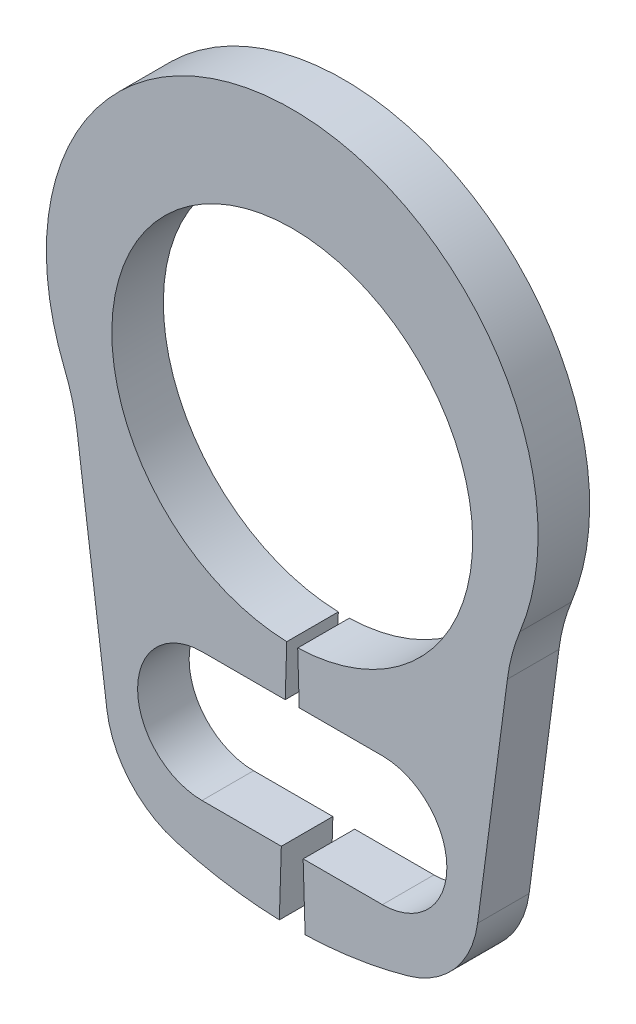
SolidWorks part; units mm, degrees
ref_plane "Plane1" through (0, 0, 0) normal (0, 0, 1) x (1, 0, 0)
ref_plane "Plane2" through (0, 0, 0) normal (0, 1, 0) x (1, 0, 0)
ref_plane "Plane3" through (0, 0, 0) normal (1, 0, 0) x (0, 0, -1)
sketch "Clipboard" plane through (0, 0, 0) normal (0, 0, 1) x (1, 0, 0)
  line L0 (0, 0) -> (0.8, 0)
  line L1 (0, 0) -> (0, 0.4)
  line L2 (0, 0) -> (0, -1.9)
  circle A0 centre (0, 0) radius 0.5
  circle A1 centre (0, 0) radius 1.5
  dimension "HoleDia" = 1
  dimension "ShaftDia" = 3
  dimension "LargeSection" = 0.8
  dimension "SmallSection" = 0.4
  dimension "LugSection" = 1.9
sketch "BodySke" plane through (0, 0, 0) normal (0, 0, 1) x (1, 0, 0)
  line L0 (-1.5431, 0) -> (1.5431, 0) construction
  line L1 (0, 0) -> (0, 2.2) construction
  line L2 (0.0424, -1.3994) -> (0.1, -3.2985)
  line L3 (-0.0424, -1.3994) -> (-0.1, -3.2985)
  line L4 (0, 0) -> (3.148, -0.99) construction
  line L5 (0, 0) -> (-3.148, -0.99) construction
  line L7 (1.6697, -0.7954) -> (1.4386, -2.5514)
  line L8 (-1.6697, -0.7954) -> (-1.4386, -2.5514)
  circle A0 centre (0, 0) radius 1.4 construction
  arc A1 (0.0424, -1.3994) -> (-0.0424, -1.3994) centre (0, 0) ccw
  arc A2 (1.7171, -0.54) -> (-1.7171, -0.54) centre (0, 0.292) ccw construction
  arc A3 (0.1, -3.2985) -> (0.8994, -3.1751) centre (0, 0) ccw
  arc A4 (1.7671, -0.4277) -> (1.6697, -0.7954) centre (3.148, -0.99) ccw
  arc A5 (-1.6697, -0.7954) -> (-1.7671, -0.4277) centre (-3.148, -0.99) ccw
  arc A6 (-0.8994, -3.1751) -> (-0.1, -3.2985) centre (0, 0) ccw
  arc A7 (1.7671, -0.4277) -> (-1.7671, -0.4277) centre (0, 0.292) ccw
  arc A8 (-1.5312, -1.8481) -> (1.5312, -1.8481) centre (0, 0) ccw construction
  circle A9 centre (0.7, -2.2956) radius 0.5
  circle A10 centre (-0.7, -2.2956) radius 0.5
  arc A11 (1.4386, -2.5514) -> (0.8994, -3.1751) centre (0.695, -2.4535) cw
  arc A12 (-1.4386, -2.5514) -> (-0.8994, -3.1751) centre (-0.695, -2.4535) ccw
  point P28 (1.3798, -2.9977)
  point P31 (-1.3798, -2.9977)
  dimension "GrooveDia" = 2.8
  dimension "D3" = 0.75
  dimension "LugRad" = 3.3
  dimension "HoleOffsetRad" = 2.4
  dimension "HoleDia" = 1
  dimension "D2" = 15
  dimension "LargeRad" = 2.2
  dimension "SmallRad" = 1.8
  dimension "Gap" = 0.2
  dimension "SmallAngle" = 145.083
  dimension "HoleSpacing" = 1.4
extrude "Body" add sketch "BodySke" against normal blind 0.4
sketch "NotSke" plane through (0, 0, 0) normal (0, 0, 1) x (1, 0, 0)
  line L0 (0.7, -1.7956) -> (0.7, -2.7956)
  line L1 (0.7, -2.7956) -> (-0.7, -2.7956)
  line L2 (-0.7, -2.7956) -> (-0.7, -1.7956)
  line L3 (-0.7, -1.7956) -> (0.7, -1.7956)
  circle A0 centre (0.7, -2.2956) radius 0.5 construction
  circle A1 centre (-0.7, -2.2956) radius 0.5 construction
extrude "Notch" cut sketch "NotSke" against normal through all
sketch "UnlSke" plane through (0, 0, 0) normal (0, 0, 1) x (1, 0, 0)
  line L0 (-1.599, -2.8867) -> (-0.6784, -1.2247)
  line L1 (1.599, -2.8867) -> (0.6784, -1.2247)
  arc A0 (0.6784, -1.2247) -> (-0.6784, -1.2247) centre (0, 0) ccw
  arc A1 (1.599, -2.8867) -> (-1.599, -2.8867) centre (0, 0) ccw
  arc A2 (0.1, -3.2985) -> (0.8994, -3.1751) centre (0, 0) ccw construction
  arc A3 (0.0424, -1.3994) -> (-0.0424, -1.3994) centre (0, 0) ccw construction
  circle A4 centre (-0.7, -2.2956) radius 0.5 construction
  circle A5 centre (0.7, -2.2956) radius 0.5 construction
extrude "Unlug" [suppressed] add sketch "UnlSke" against normal through all
equation "' \"ShaftDia@Clipboard\" = 3"
equation "' \"Thickness@Body\" = 0.4"
equation "' \"GrooveDia@BodySke\" = 2.8"
equation "' \"LugSection@Clipboard\" = 1.9"
equation "' \"LargeSection@Clipboard\" = 0.8"
equation "' \"HoleDia@Clipboard\" = 1.0"
equation "' \"ShaftDia@Clipboard\" = 10"
equation "' \"Thickness@Body\" = 1.0"
equation "' \"GrooveDia@BodySke\" = 9.6"
equation "' \"LugSection@Clipboard\" = 3.3"
equation "' \"LargeSection@Clipboard\" = 1.8"
equation "' \"HoleDia@Clipboard\" = 1.5"
equation "\"SmallSection@Clipboard\" = \"LargeSection@Clipboard\" * 0.5"
equation "\"Gap@BodySke\" =  \"Thickness@Body\" / 2"
equation "\"LargeRad@BodySke\" =  \"GrooveDia@BodySke\" / 2 +  \"LargeSection@Clipboard\""
equation "\"SmallRad@BodySke\" =  \"GrooveDia@BodySke\" / 2 +  \"SmallSection@Clipboard\""
equation "\"LugRad@BodySke\" = \"GrooveDia@BodySke\" / 2 + \"LugSection@Clipboard\""
equation "\"HoleOffsetRad@BodySke\" = (  \"ShaftDia@Clipboard\" / 2 + \"LugRad@BodySke\" ) / 2"
equation "\"HoleSpacing@BodySke\" = \"Gap@BodySke\"  * 2 +  \"HoleDia@Clipboard\""
equation "\"HoleDia@BodySke\" =  \"HoleDia@Clipboard\""
equation "\"SmallAngle@BodySke\" = atn(\"HoleSpacing@BodySke\" / 2 / sqr(\"HoleOffsetRad@BodySke\"  * \"HoleOffsetRad@BodySke\" - (\"HoleSpacing@BodySke\" / 2) * (\"HoleSpacing@BodySke\" / 2) ))  * 7 *  (\"LargeRad@BodySke\" / \"SmallRad@BodySke\")* ( 180 / 3.141593)"
